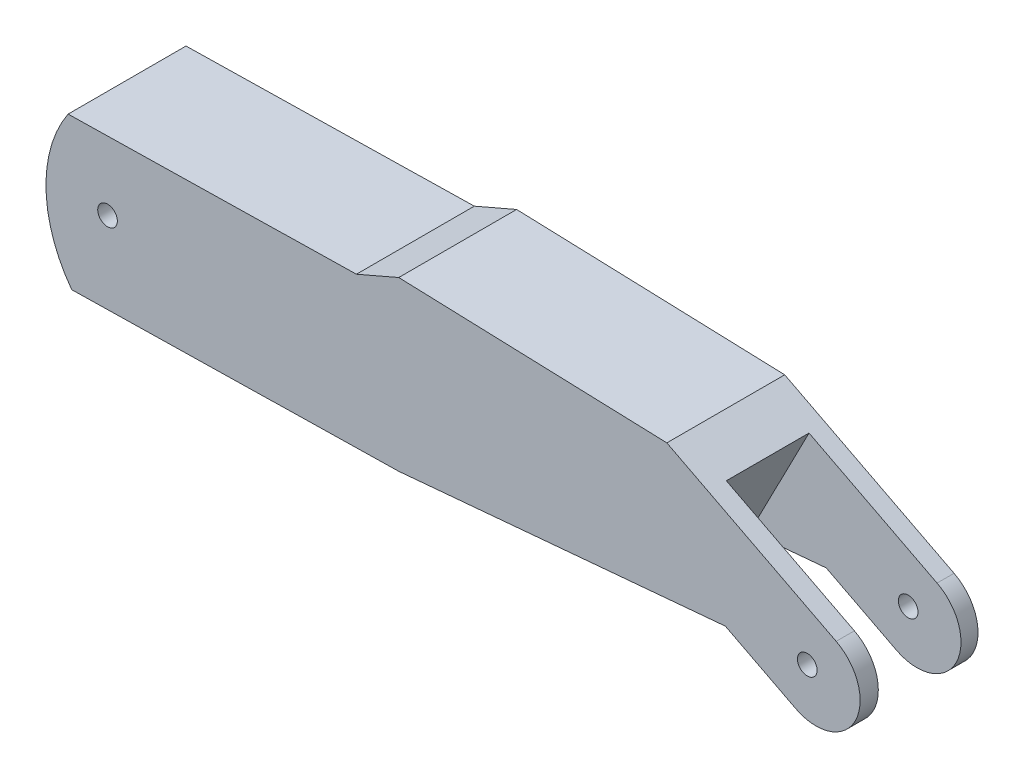
SolidWorks part; units mm, degrees
ref_plane "Front Plane" through (0, 0, 0) normal (0, 0, 1) x (1, 0, 0)
ref_plane "Top Plane" through (0, 0, 0) normal (0, 1, 0) x (1, 0, 0)
ref_plane "Right Plane" through (0, 0, 0) normal (1, 0, 0) x (0, 0, -1)
sketch "Sketch1" plane through (0, 0, 0) normal (0, 0, 1) x (1, 0, 0)
  line L0 (-858.6496, -198.2387) -> (-60.0625, 92.8949) construction
  line L1 (-221.3215, 37.0521) -> (-74.5631, 39.8504)
  line L2 (-74.5631, 39.8504) -> (-53.022, 49.1707)
  line L3 (-53.022, 49.1707) -> (83.4319, 44.5106)
  line L4 (83.4319, 44.5106) -> (169.6199, 0.1252)
  line L5 (-219.4559, -39.4364) -> (-53.022, -36.2628)
  line L6 (-53.022, -36.2628) -> (113.2173, -21.3858)
  line L7 (113.2173, -21.3858) -> (149.0414, -39.8345)
  arc A0 (-221.3215, 37.0521) -> (-219.4559, -39.4364) centre (-166.3761, 0.1252) ccw
  arc A1 (169.6199, 0.1252) -> (149.0414, -39.8345) centre (159.3306, -19.8547) cw
extrude "Boss-Extrude1" add sketch "Sketch1" along normal blind 60
sketch "Sketch6" plane through (35.6059, 69.1401, 0) normal (0.4578, 0.889, 0) x (0.889, -0.4578, 0)
  line L1 (77.4378, -50.7328) -> (181.8036, -50.7328)
  line L2 (77.4378, -50.7328) -> (77.4378, -8.6544)
  line L3 (77.4378, -8.6544) -> (181.8036, -8.6544)
  line L4 (181.8036, -50.7328) -> (181.8036, -8.6544)
extrude "Cut-Extrude1" cut sketch "Sketch6" against normal blind 60
sketch "Sketch7" plane through (0, 0, 60) normal (0, 0, 1) x (1, 0, 0)
  line L1 (-74.5631, 39.8504) -> (-221.3215, 37.0521) construction
  circle A0 centre (-201.234, 2.4287) radius 5
  point P4 (-232.0148, -8.4858)
  dimension "D1" = 35
  dimension "D2" = 10
extrude "Cut-Extrude2" cut sketch "Sketch7" against normal blind 80
sketch "Sketch8" plane through (0, 0, 60) normal (0, 0, 1) x (1, 0, 0)
  circle A0 centre (154.9125, -17.5137) radius 5
  arc A2 (149.0414, -39.8345) -> (169.6199, 0.1252) centre (159.3306, -19.8547) ccw construction
  point P2 (0, 0)
  point P3 (0, 0)
  dimension "D1" = 10
  dimension "D2" = 5
extrude "Cut-Extrude3" cut sketch "Sketch8" against normal blind 80
